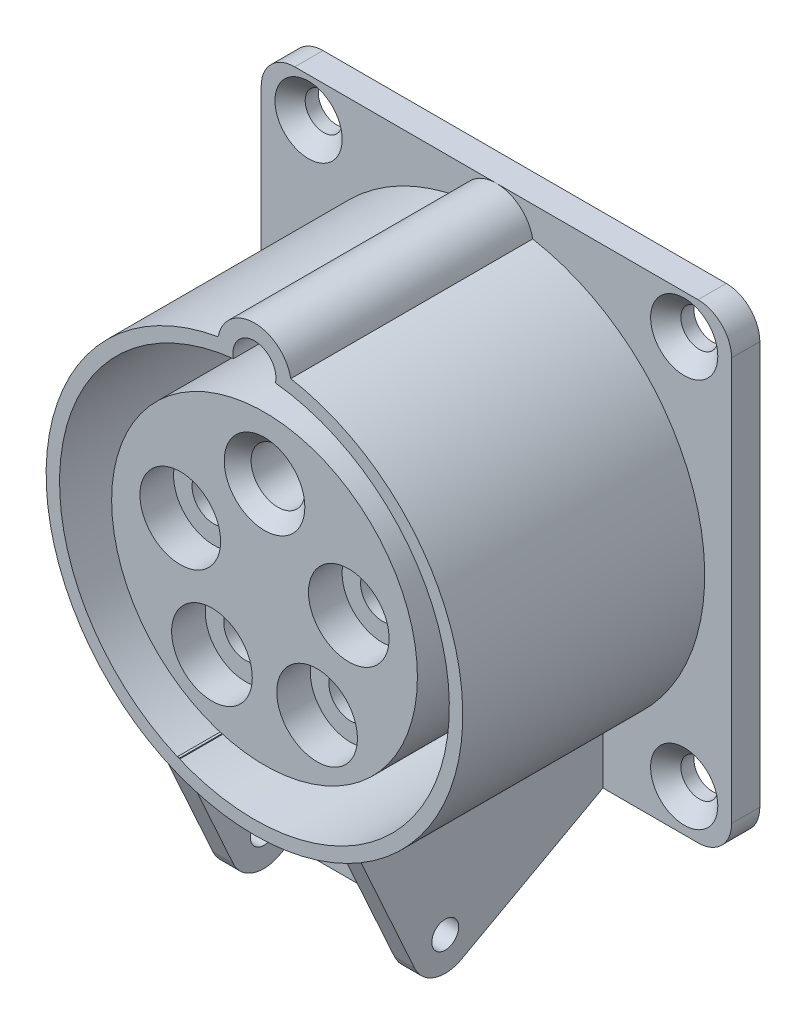
SolidWorks part; units mm, degrees
material "Nylon 101"
ref_plane "Front Plane" through (0, 0, 0) normal (0, 0, 1) x (1, 0, 0)
ref_plane "Top Plane" through (0, 0, 0) normal (0, 1, 0) x (1, 0, 0)
ref_plane "Right Plane" through (0, 0, 0) normal (1, 0, 0) x (0, 0, -1)
sketch "Sketch1" plane through (0, 0, 0) normal (0, 0, 1) x (1, 0, 0)
  line L0 (-264.7837, -302.4836) -> (-263.2063, -362.7236) construction
  line L5 (-0.8649, 2.2379) -> (-0.8649, -21.9058) construction
  circle A3 centre (20.9533, 12.2276) radius 4.0732
  arc A5 (17.615, -6.8714) -> (12.8025, 3.1692) centre (13.1289, -2.848) ccw
  circle A6 centre (10.8673, -18.8927) radius 3.3478
  circle A14 centre (7.8665, 14.1463) radius 6.0261
  circle A16 centre (13.1289, -2.848) radius 6.0261
  circle A18 centre (-14.8586, -2.848) radius 6.0261
  circle A22 centre (-22.683, 12.2276) radius 4.0732
  circle A25 centre (-9.5963, 14.1463) radius 6.0261
  arc A27 (-15.6157, 13.8645) -> (-7.5149, 19.8015) centre (-9.5963, 14.1463) cw
  circle A28 centre (10.8673, -18.8927) radius 2.5
  circle A29 centre (-0.8649, -14.6917) radius 7.21
  circle A30 centre (-0.8649, 2.9253) radius 22.75
  circle A31 centre (-0.8649, 2.9253) radius 25.25
  circle A32 centre (-0.8649, 2.9253) radius 27.5
  circle A33 centre (-0.8649, 2.9253) radius 30.15
  circle A34 centre (-0.8649, 2.9253) radius 28.75
  circle A35 centre (-14.8586, -2.848) radius 7.3261
  circle A36 centre (-14.8586, -2.848) radius 4.7261
  circle A37 centre (-14.8586, -2.848) radius 8.6261
  circle A41 centre (-9.5963, 14.1463) radius 7.3261
  circle A42 centre (-9.5963, 14.1463) radius 4.7261
  circle A43 centre (-9.5963, 14.1463) radius 8.6261
  circle A44 centre (13.1289, -2.848) radius 4.7261
  circle A45 centre (13.1289, -2.848) radius 7.3261
  circle A46 centre (13.1289, -2.848) radius 8.6261
  circle A47 centre (7.8665, 14.1463) radius 4.7261
  circle A48 centre (7.8665, 14.1463) radius 7.3261
  circle A49 centre (7.8665, 14.1463) radius 8.6261
  circle A50 centre (-0.8649, -14.6917) radius 8.71
  circle A51 centre (-0.8649, -14.6917) radius 6.71
  point P36 (-0.8649, 2.9253)
  point P40 (-0.8649, -26.7764)
  dimension "D1" = 5
  dimension "D2" = 14.42
  dimension "D3" = 45.5
  dimension "D4" = 50.5
  dimension "D5" = 55
  dimension "D6" = 60.3
  dimension "D7" = 57.5
  dimension "D8" = 1.3
  dimension "D9" = 1.3
  dimension "D10" = 12.0521
  dimension "D11" = 1.3
  dimension "D12" = 1.5
  dimension "D13" = 0.5
sketch "Sketch2" plane through (0, 0, 0) normal (0, 0, 1) x (1, 0, 0)
  arc A0 (-6.2684, 33.4507) -> (4.5387, 33.4507) centre (-0.8649, 2.9253) ccw
  arc A1 (4.5387, 33.4507) -> (-6.2684, 33.4507) centre (-0.8649, 32.4253) ccw
  dimension "D1" = 62
  dimension "D2" = 29.5
  dimension "D3" = 11
extrude "Boss-Extrude1" add sketch "Sketch2" along normal blind 36
sketch "Sketch3" plane through (0, 0, 36) normal (0, 0, 1) x (1, 0, 0)
  line L1 (-0.8649, 2.9253) -> (-0.8649, 50002.9253) construction
  arc A0 (-3.9941, 31.756) -> (2.2644, 31.756) centre (-0.8649, 2.9253) ccw
  arc A1 (2.2644, 31.756) -> (-3.9941, 31.756) centre (-0.8649, 32.4253) ccw
  arc A2 (-6.2684, 33.4507) -> (4.5387, 33.4507) centre (-0.8649, 2.9253) ccw construction
  circle A4 centre (-0.8649, 2.9253) radius 22.75
  dimension "D1" = 58
  dimension "D3" = 6.4
  dimension "D4" = 45.5
  dimension "D2" = 29.5
sketch "Sketch4" plane through (0, 0, 0) normal (0, 0, -1) x (-1, 0, 0)
  line L1 (-34.1351, -32.0747) -> (35.8649, -32.0747)
  line L2 (-34.1351, -32.0747) -> (-34.1351, 37.9253)
  line L3 (-34.1351, 37.9253) -> (35.8649, 37.9253)
  line L4 (35.8649, -32.0747) -> (35.8649, 37.9253)
  line L5 (-34.1351, -32.0747) -> (35.8649, 37.9253) construction
  line L6 (-34.1351, 37.9253) -> (35.8649, -32.0747) construction
  circle A0 centre (-27.0851, -25.8247) radius 2.75
  circle A1 centre (-27.0851, 32.11) radius 2.75
  circle A2 centre (28.8149, 32.11) radius 2.75
  circle A3 centre (28.8149, -25.8247) radius 2.75
  point P0 (0.8649, 2.9253)
  dimension "D2" = 5.5
  dimension "D1" = 70
extrude "Boss-Extrude2" add sketch "Sketch4" along normal blind 4.2
fillet "Fillet1" radius 5 4 edges at (-35.8649, 37.9253, -2.1) (-35.8649, -32.0747, -2.1) (34.1351, -32.0747, -2.1) (34.1351, 37.9253, -2.1)
extrude "Cut-Extrude1" cut sketch "Sketch3" against normal blind 38.5
sketch "Sketch7" plane through (0, 0, 36) normal (0, 0, 1) x (1, 0, 0)
  circle A0 centre (-0.8649, 2.9253) radius 22.75
  circle A1 centre (-0.8649, 2.9253) radius 22.75 construction
extrude "Cut-Extrude2" cut sketch "Sketch7" against normal blind 1.5 contours A0
sketch "Sketch8" plane through (0, 0, 34.5) normal (0, 0, 1) x (1, 0, 0)
  line L0 (246.2964, 307.8954) -> (244.7189, 368.1354) construction
  line L5 (-0.8649, 3.6126) -> (-0.8649, 27.7563) construction
  circle A3 centre (-22.683, -6.3771) radius 4.0732
  arc A5 (-19.3448, 12.722) -> (-14.5323, 2.6814) centre (-14.8586, 8.6986) ccw
  circle A6 centre (-12.597, 24.7432) radius 3.3478
  circle A14 centre (-9.5963, -8.2957) radius 6.0261
  circle A16 centre (-14.8586, 8.6986) radius 6.0261
  circle A18 centre (13.1289, 8.6986) radius 6.0261
  circle A22 centre (20.9533, -6.3771) radius 4.0732
  circle A25 centre (7.8665, -8.2957) radius 6.0261
  arc A27 (13.886, -8.014) -> (5.7852, -13.9509) centre (7.8665, -8.2957) cw
  circle A28 centre (-12.597, 24.7432) radius 2.5
  circle A29 centre (-0.8649, 20.5423) radius 7.21
  circle A30 centre (-0.8649, 2.9253) radius 22.75
  circle A31 centre (-0.8649, 2.9253) radius 25.25
  circle A32 centre (-0.8649, 2.9253) radius 27.5
  circle A33 centre (-0.8649, 2.9253) radius 30.15
  circle A34 centre (-0.8649, 2.9253) radius 28.75
  circle A35 centre (13.1289, 8.6986) radius 7.3261
  circle A36 centre (13.1289, 8.6986) radius 4.7261
  circle A37 centre (13.1289, 8.6986) radius 8.6261
  circle A41 centre (7.8665, -8.2957) radius 7.3261
  circle A42 centre (7.8665, -8.2957) radius 4.7261
  circle A43 centre (7.8665, -8.2957) radius 8.6261
  circle A44 centre (-14.8586, 8.6986) radius 4.7261
  circle A45 centre (-14.8586, 8.6986) radius 7.3261
  circle A46 centre (-14.8586, 8.6986) radius 8.6261
  circle A47 centre (-9.5963, -8.2957) radius 4.7261
  circle A48 centre (-9.5963, -8.2957) radius 7.3261
  circle A49 centre (-9.5963, -8.2957) radius 8.6261
  circle A50 centre (-0.8649, 20.5423) radius 8.71
  circle A51 centre (-0.8649, 20.5423) radius 6.71
  point P36 (-0.8649, 2.9253)
  point P40 (-0.8649, 32.627)
  dimension "D1" = 5
  dimension "D2" = 14.42
  dimension "D3" = 45.5
  dimension "D4" = 50.5
  dimension "D5" = 55
  dimension "D6" = 60.3
  dimension "D7" = 57.5
  dimension "D8" = 1.3
  dimension "D9" = 1.3
  dimension "D10" = 12.0521
  dimension "D11" = 1.3
  dimension "D12" = 1.5
  dimension "D13" = 0.5
sketch "Sketch9" plane through (0, 0, 34.5) normal (0, 0, 1) x (1, 0, 0)
  line L0 (-236.4959, -273.0632) -> (-235.0824, -327.0447) construction
  line L9 (-0.8649, 2.6442) -> (-0.8649, 50002.6442) construction
  line L18 (29.1351, -32.0747) -> (-30.8649, -32.0747) construction
  arc A2 (4.5387, 33.4507) -> (-6.2684, 33.4507) centre (-0.8649, 32.4253) ccw construction
  arc A6 (-9.4708, 10.2893) -> (-8.1774, 2.8106) centre (-13.4036, 5.7579) ccw
  circle A8 centre (-0.8649, 16.4253) radius 4
  circle A15 centre (-8.6855, -9.4681) radius 6
  circle A17 centre (-13.4036, 5.7579) radius 6
  circle A19 centre (11.6738, 5.7579) radius 6
  circle A26 centre (6.9558, -9.4681) radius 6
  point P12 (-0.8649, 37.9253)
  point P39 (-0.8649, 2.0283)
  point P43 (-0.8649, 28.6442)
  dimension "D2" = 25.0774
  dimension "D3" = 15.6413
  dimension "D5" = 12
  dimension "D6" = 25.8934
  dimension "D7" = 21.5
  dimension "D11" = 8
  dimension "D9" = 12
  dimension "D1" = 54
  dimension "D4" = 10.6674
extrude "Cut-Extrude3" cut sketch "Sketch9" against normal blind 5 contours A17 | A19 | A26 | A15
sketch "Sketch11" plane through (0, 0, 29.5) normal (0, 0, 1) x (1, 0, 0)
  circle A0 centre (11.6738, 5.7579) radius 3.25
  circle A1 centre (-13.4036, 5.7579) radius 3.25
  circle A2 centre (-8.6855, -9.4681) radius 3.25
  circle A3 centre (6.9558, -9.4681) radius 3.25
  circle A4 centre (11.6738, 5.7579) radius 6 construction
  circle A5 centre (-13.4036, 5.7579) radius 6 construction
  circle A6 centre (-8.6855, -9.4681) radius 6 construction
  circle A7 centre (6.9558, -9.4681) radius 6 construction
  dimension "D1" = 6.5
extrude "Cut-Extrude4" cut sketch "Sketch11" against normal blind 12
sketch "Sketch12" plane through (0, 0, 17.5) normal (0, 0, 1) x (1, 0, 0)
  circle A0 centre (11.6738, 5.7579) radius 4
  circle A1 centre (6.9558, -9.4681) radius 4
  circle A2 centre (-8.6855, -9.4681) radius 4
  circle A3 centre (-13.4036, 5.7579) radius 4
  circle A4 centre (-13.4036, 5.7579) radius 3.25 construction
  circle A5 centre (-8.6855, -9.4681) radius 3.25 construction
  circle A6 centre (6.9558, -9.4681) radius 3.25 construction
  circle A7 centre (11.6738, 5.7579) radius 3.25 construction
  dimension "D1" = 8
extrude "Cut-Extrude5" cut sketch "Sketch12" against normal through all contours A0 | A1 | A2 | A3
sketch "Sketch14" plane through (0, 0, 34.5) normal (0, 0, 1) x (1, 0, 0)
  line L0 (-0.8649, 17.6361) -> (-0.8649, 50017.6361) construction
  arc A0 (-9.4708, 10.2893) -> (-8.1774, 2.8106) centre (-13.4036, 5.7579) ccw
  circle A1 centre (-0.8649, 16.4253) radius 4
  circle A2 centre (-8.6855, -9.4681) radius 6
  circle A3 centre (-13.4036, 5.7579) radius 6
  circle A4 centre (11.6738, 5.7579) radius 6
  circle A5 centre (6.9558, -9.4681) radius 6
  circle A6 centre (11.6738, 5.7579) radius 6 construction
  point P10 (-0.8649, 17.0202)
  point P11 (-0.8649, 43.6361)
  dimension "D1" = 8
  dimension "D2" = 12
  dimension "D3" = 12
  dimension "D4" = 25.0774
  dimension "D5" = 15.6413
  dimension "D6" = 10.6674
  dimension "D7" = 25.8934
extrude "Cut-Extrude6" cut sketch "Sketch14" against normal blind 8 contours A1
chamfer "Chamfer1" distance 2 angle 45 1 edges at (3.1351, 16.4253, 34.5)
sketch "Sketch15" plane through (0, 0, 26.5) normal (0, 0, 1) x (1, 0, 0)
  circle A0 centre (-0.8649, 16.4253) radius 5
  circle A1 centre (-0.8649, 16.4253) radius 4 construction
  dimension "D1" = 10
extrude "Cut-Extrude7" cut sketch "Sketch15" against normal through all
sketch "Sketch16" plane through (0, 0, -4.2) normal (0, 0, -1) x (-1, 0, 0)
  line L0 (0.8649, 37.9253) -> (0.8649, -32.0747) construction
  line L1 (30.8649, 37.9253) -> (-29.1351, 37.9253) construction
  line L2 (-29.1351, -32.0747) -> (30.8649, -32.0747) construction
  line L3 (-34.1351, 2.9253) -> (35.8649, 2.9253) construction
  line L4 (-34.1351, 32.9253) -> (-34.1351, -27.0747) construction
  line L5 (35.8649, -27.0747) -> (35.8649, 32.9253) construction
  circle A0 centre (0.8649, 2.9253) radius 27.5
  circle A1 centre (0.8649, 2.9253) radius 25.2
  dimension "D1" = 55
  dimension "D2" = 50.4
extrude "Boss-Extrude3" add sketch "Sketch16" along normal blind 2.7 contours A0 | A1
ref_plane "Plane1" through (15, 0, 0) normal (1, 0, 0) x (0, 0, -1)
sketch "Sketch17" plane through (15, 0, 0) normal (1, 0, 0) x (0, 0, -1)
  line L0 (0, 33.4507) -> (0, -28.0747) construction
  line L4 (-36, 33.4507) -> (-36, -28.0747) construction
  line L5 (-36, 33.4507) -> (-36, -39.6507) construction
  line L6 (0, 33.4507) -> (0, -39.6507) construction
  line L11 (0, -23.7075) -> (-36, -23.7075)
  line L12 (-36, 29.5581) -> (0, 29.5581)
  line L13 (-36, 29.5581) -> (0, 29.5581)
  line L14 (0, -23.7075) -> (-36, -23.7075)
  line L15 (0, 37.9253) -> (0, 29.5581)
  line L16 (0, -23.7075) -> (0, -32.0747)
  line L17 (0, -23.7075) -> (0, -32.0747)
  line L18 (0, 37.9253) -> (0, 29.5581)
  line L19 (-36, -23.7075) -> (0, -23.7075)
  line L20 (-36, -23.7075) -> (-25.8, -46.2075)
  line L21 (0, -23.7075) -> (0, -32.0747)
  line L22 (-25.8, -46.2075) -> (0, -32.0747)
  circle A0 centre (-23.4726, -39.2316) radius 2
  dimension "D5" = 4
  dimension "D1" = 30
  dimension "D2" = 22.5
  dimension "D3" = 5
  dimension "D4" = 5
extrude "Boss-Extrude4" add sketch "Sketch17" against normal blind 3 contours L20 L22 L17 L14 A0
mirror "Mirror1" about plane through (0, 0, 0) normal (1, 0, 0) of "Boss-Extrude4"
sketch "Sketch19" plane through (0, 0, 0) normal (1, 0, 0) x (0, 0, -1)
  line L0 (0, 32.9253) -> (0, -27.0747) construction
  line L1 (0, 32.9253) -> (0, -27.0747) construction
  line L2 (-34.9581, -26.0058) -> (0, -26.0058) construction
  line L3 (0, -25.2792) -> (0, -28.0747) construction
  line L4 (0, -25.2792) -> (-35.2875, -25.2792) construction
  line L5 (-36, -23.7075) -> (-35.2875, -25.2792) construction
  line L6 (-35.2875, -25.2792) -> (-25.8, -46.2075)
  line L7 (0, -25.2792) -> (-35.2875, -25.2792)
  line L8 (0, -32.0747) -> (0, -25.2792)
  line L9 (-25.8, -46.2075) -> (0, -32.0747)
  line L10 (-35.2875, -25.2792) -> (-25.8, -46.2075) construction
  line L11 (0, -25.2792) -> (-35.2875, -25.2792) construction
  line L12 (0, -32.0747) -> (0, -25.2792) construction
  line L13 (-25.8, -46.2075) -> (0, -32.0747) construction
  line L14 (-36, 33.4507) -> (-36, -28.0747) construction
  line L15 (-36, 33.4507) -> (0, 33.4507) construction
  line L16 (0, 33.4507) -> (0, -24.6645) construction
  line L18 (-35.5662, -24.6645) -> (-34.9581, -26.0058) construction
  line L19 (-36, 33.4507) -> (-36, -23.7075) construction
  line L21 (0, 33.4507) -> (0, -23.7075) construction
  line L22 (0, 33.4507) -> (-36, 33.4507) construction
  line L23 (-36, 33.4507) -> (-36, -23.7075) construction
  line L24 (0, -26.0058) -> (0, -32.0747)
  line L25 (0, 33.4507) -> (0, -23.7075) construction
  line L26 (0, 33.4507) -> (-36, 33.4507)
  line L27 (-34.9581, -26.0058) -> (0, -26.0058) construction
  line L28 (0, -25.2792) -> (0, -28.0747) construction
  line L29 (0, -25.2792) -> (-35.2875, -25.2792) construction
  line L30 (-36, -23.7075) -> (-35.2875, -25.2792) construction
  line L31 (-36, 33.4507) -> (-36, -28.0747) construction
  line L32 (-36, 33.4507) -> (0, 33.4507)
  line L33 (0, 33.4507) -> (0, -24.6645)
  line L34 (0, -26.0058) -> (-18, -26.0058)
  line L35 (-35.5662, -24.6645) -> (-34.9581, -26.0058) construction
  line L36 (0, -32.0747) -> (-18, -41.9348)
  line L37 (-18, -26.0058) -> (-18, -41.9348)
  dimension "D2" = 18
  dimension "D1" = 0
extrude "Boss-Extrude5" add sketch "Sketch19" along normal blind 0.8 and the other way blind 0.8 contours L24 L34 L37 L36
sketch "Sketch20" plane through (0, -24.6716, -13.5147) normal (0, -0.877, -0.4804) x (1, 0, 0)
  line L0 (-0.8, 35.9332) -> (0.8, 35.9332) construction
  line L1 (12, 44.8268) -> (12, 15.4095) construction
  line L2 (-12, 44.8268) -> (-12, 15.4095) construction
  line L3 (-0.8, 35.9332) -> (0.8, 35.9332) construction
  line L4 (12, 44.8268) -> (12, 15.4095) construction
  line L5 (-12, 44.8268) -> (-12, 15.4095) construction
  line L6 (-12, 15.4095) -> (12, 15.4095)
  line L7 (-12, 15.4095) -> (-12, 37.9332)
  line L8 (12, 15.4095) -> (12, 37.9332)
  line L9 (-12, 37.9332) -> (12, 37.9332)
  line L10 (29.1351, 15.4095) -> (15, 15.4095)
  line L11 (15, 15.4095) -> (12, 15.4095)
  line L12 (12, 15.4095) -> (0.8, 15.4095)
  line L13 (0.8, 15.4095) -> (-0.8, 15.4095)
  line L14 (-0.8, 15.4095) -> (-12, 15.4095)
  line L15 (-12, 15.4095) -> (-15, 15.4095)
  line L16 (-15, 15.4095) -> (-30.8649, 15.4095)
  line L17 (-30.8649, 15.4095) -> (-30.8649, 11.726)
  line L18 (-30.8649, 11.726) -> (29.1351, 11.726)
  line L19 (29.1351, 11.726) -> (29.1351, 15.4095)
  line L20 (29.1351, 15.4095) -> (15, 15.4095) construction
  line L21 (15, 15.4095) -> (12, 15.4095) construction
  line L22 (12, 15.4095) -> (0.8, 15.4095) construction
  line L23 (0.8, 15.4095) -> (-0.8, 15.4095) construction
  line L24 (-0.8, 15.4095) -> (-12, 15.4095) construction
  line L25 (-12, 15.4095) -> (-15, 15.4095) construction
  line L26 (-15, 15.4095) -> (-30.8649, 15.4095) construction
  line L27 (-30.8649, 15.4095) -> (-30.8649, 11.726) construction
  line L28 (-30.8649, 11.726) -> (29.1351, 11.726) construction
  line L29 (29.1351, 11.726) -> (29.1351, 15.4095) construction
  dimension "D2" = 2
  dimension "D1" = 0
extrude "Boss-Extrude6" add sketch "Sketch20" along direction (0, -1, 0) on the side against the normal blind 2 contours L6 L7 L9 L8
fillet "Fillet2" radius 5 2 edges at (-13.5, -46.2075, 25.8) (13.5, -46.2075, 25.8)
sketch "Sketch22" plane through (0, 0, 36) normal (0, 0, 1) x (1, 0, 0)
  arc A3 (4.5387, 33.4507) -> (-6.2684, 33.4507) centre (-0.8649, 32.4253) ccw
  arc A4 (-6.2684, 33.4507) -> (15, -23.7075) centre (-0.8649, 2.9253) ccw
  arc A5 (15, -23.7075) -> (4.5387, 33.4507) centre (-0.8649, 2.9253) ccw
  arc A6 (4.5387, 33.4507) -> (-6.2684, 33.4507) centre (-0.8649, 32.4253) ccw
  arc A7 (-6.2684, 33.4507) -> (15, -23.7075) centre (-0.8649, 2.9253) ccw
  arc A8 (15, -23.7075) -> (4.5387, 33.4507) centre (-0.8649, 2.9253) ccw
  dimension "D1" = 0
ref_plane "Plane2" through (12, -40.8957, 19.7541) normal (1, 0, 0) x (0, 0, -1)
sketch "Sketch23" plane through (0, 0, 0) normal (1, 0, 0) x (0, 0, -1)
  line L6 (-34.9581, -26.0058) -> (-28.0265, -41.296)
  line L7 (-21.0705, -43.6168) -> (-19.7541, -42.8957)
  line L8 (-19.7541, -42.8957) -> (-19.7541, -40.8957)
  line L9 (-19.7541, -40.8957) -> (0, -30.0747)
  line L10 (0, -30.0747) -> (0, -26.0058)
  line L11 (0, -26.0058) -> (-34.9581, -26.0058)
  line L12 (-34.9581, -26.0058) -> (-28.0265, -41.296) construction
  line L13 (-21.0705, -43.6168) -> (-19.7541, -42.8957) construction
  line L14 (-19.7541, -42.8957) -> (-19.7541, -40.8957) construction
  line L15 (-19.7541, -40.8957) -> (0, -30.0747) construction
  line L16 (0, -30.0747) -> (0, -26.0058) construction
  line L17 (0, -26.0058) -> (-34.9581, -26.0058) construction
  circle A0 centre (-23.4726, -39.2316) radius 2 construction
  arc A1 (-28.0265, -41.296) -> (-21.0705, -43.6168) centre (-23.4726, -39.2316) ccw
  arc A2 (-28.0265, -41.296) -> (-21.0705, -43.6168) centre (-23.4726, -39.2316) ccw construction
  circle A3 centre (-23.4726, -39.2316) radius 2 construction
  dimension "D1" = 0
chamfer "Chamfer2" distance 2.25 angle 45 4 edges at (-31.5649, -25.8247, 0) (24.3351, -25.8247, 0) (24.3351, 32.11, 0) (-31.5649, 32.11, 0)
